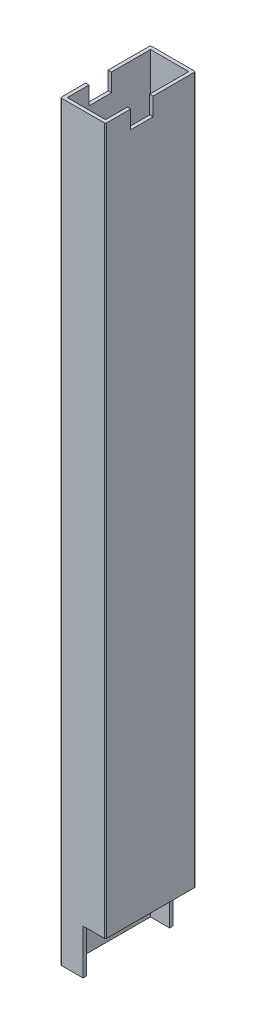
SolidWorks part; units mm, degrees
ref_plane "Front Plane" through (0, 0, 0) normal (0, 0, 1) x (1, 0, 0)
ref_plane "Top Plane" through (0, 0, 0) normal (0, 1, 0) x (1, 0, 0)
ref_plane "Right Plane" through (0, 0, 0) normal (1, 0, 0) x (0, 0, -1)
sketch "Sketch1" plane through (0, 0, 0) normal (0, 1, 0) x (1, 0, 0)
  line L0 (1.5, 1.5) -> (18.5, 1.5)
  line L1 (0.5, 0) -> (19.5, 0)
  line L2 (0, 0.5) -> (0, 39.5)
  line L3 (0.5, 40) -> (19.5, 40)
  line L4 (20, 0.5) -> (20, 39.5)
  line L5 (18.5, 1.5) -> (18.5, 38.5)
  line L6 (1.5, 38.5) -> (18.5, 38.5)
  line L7 (1.5, 1.5) -> (1.5, 38.5)
  arc A0 (19.5, 0) -> (20, 0.5) centre (19.5, 0.5) ccw
  arc A1 (0.5, 0) -> (0, 0.5) centre (0.5, 0.5) cw
  arc A2 (0, 39.5) -> (0.5, 40) centre (0.5, 39.5) cw
  arc A3 (19.5, 40) -> (20, 39.5) centre (19.5, 39.5) cw
  arc A4 (18.5, 1.5) -> (18.5, 1.5) centre (18.5, 1.5) ccw
  arc A5 (18.5, 38.5) -> (18.5, 38.5) centre (18.5, 38.5) cw
  arc A6 (1.5, 38.5) -> (1.5, 38.5) centre (1.5, 38.5) cw
  arc A7 (1.5, 1.5) -> (1.5, 1.5) centre (1.5, 1.5) cw
  point P9 (0, 0)
  dimension "D3" = 0.5
  dimension "D1" = 20
  dimension "D2" = 40
  dimension "D4" = 1.5
extrude "Boss-Extrude1" add sketch "Sketch1" along normal blind 334
sketch "Sketch2" plane through (0, 0, 0) normal (0, 0, 1) x (1, 0, 0)
  line L0 (10, 20) -> (10, 0)
  line L1 (20, 0) -> (10, 0)
  line L2 (20, 0) -> (20, 20)
  line L3 (20, 20) -> (10, 20)
  line L5 (0.5, 0) -> (19.5, 0) construction
  dimension "D1" = 20
extrude "Cut-Extrude1" cut sketch "Sketch2" against normal blind 40
sketch "Sketch3" plane through (0, 0, 0) normal (1, 0, 0) x (0, 0, -1)
  line L6 (0, 334) -> (0, 324)
  line L7 (0, 334) -> (0, 0) construction
  line L8 (0, 324) -> (19.8205, 324)
  line L9 (19.8205, 324) -> (2.5, 334)
  line L10 (39.5, 334) -> (0.5, 334) construction
  line L11 (2.5, 334) -> (0, 334)
  line L12 (17.5, 334) -> (34.8205, 324)
  line L13 (34.8205, 324) -> (40, 324)
  line L14 (40, 334) -> (40, 0) construction
  line L15 (40, 324) -> (40, 334)
  line L16 (40, 334) -> (17.5, 334)
  dimension "D1" = 15
  dimension "D2" = 10
  dimension "D3" = 30
  dimension "10" = 2.5
extrude "Cut-Extrude2" [suppressed] cut sketch "Sketch3" along normal blind 40
sketch "Sketch4" plane through (20, 0, 0) normal (1, 0, 0) x (0, 0, -1)
  line L7 (0.5, 334) -> (39.5, 334) construction
  line L14 (11.16, 334) -> (21.16, 334)
  line L15 (11.16, 334) -> (11.16, 326)
  line L16 (11.16, 326) -> (21.16, 326)
  line L17 (21.16, 334) -> (21.16, 326)
  line L18 (0, 334) -> (0, 20) construction
  dimension "D1" = 8
  dimension "D2" = 10
  dimension "D3" = 11.16
extrude "Cut-Extrude3" cut sketch "Sketch4" against normal through all
